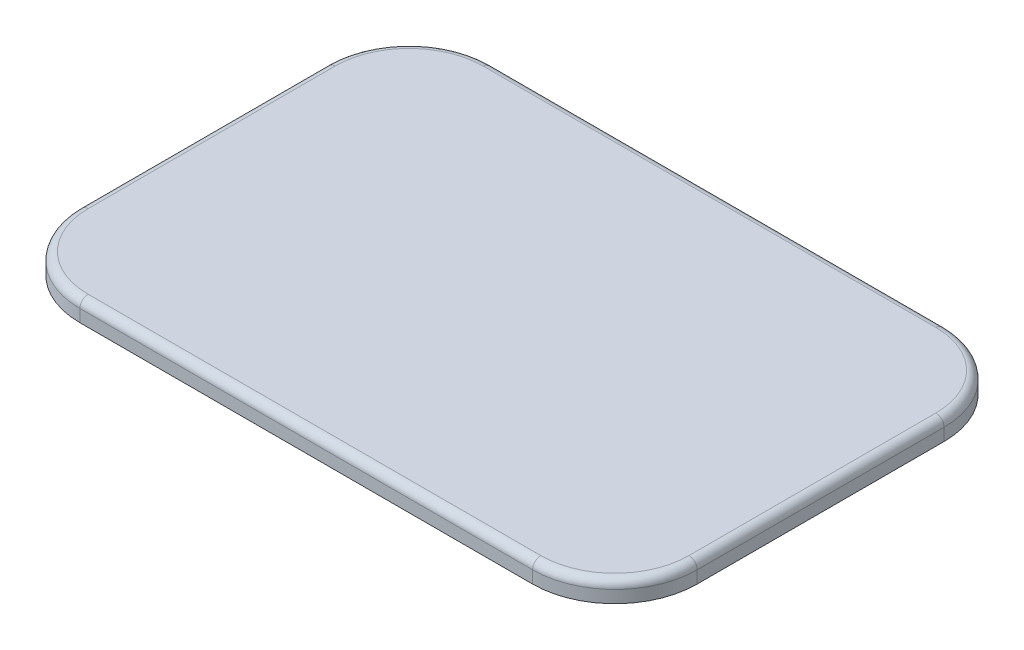
SolidWorks part; units mm, degrees
ref_plane "Płaszczyzna przednia" through (0, 0, 0) normal (0, 0, 1) x (1, 0, 0)
ref_plane "Płaszczyzna górna" through (0, 0, 0) normal (0, 1, 0) x (1, 0, 0)
ref_plane "Płaszczyzna prawa" through (0, 0, 0) normal (1, 0, 0) x (0, 0, -1)
sketch "Szkic1" plane through (0, 0, 0) normal (0, 1, 0) x (1, 0, 0)
  line L1 (-110, -100) -> (110, -100)
  line L2 (-150, -60) -> (-150, 60)
  line L3 (-110, 100) -> (110, 100)
  line L4 (150, -60) -> (150, 60)
  line L5 (-150, -100) -> (150, 100) construction
  line L6 (-150, 100) -> (150, -100) construction
  arc A0 (110, 100) -> (150, 60) centre (110, 60) cw
  arc A1 (110, -100) -> (150, -60) centre (110, -60) ccw
  arc A2 (-110, -100) -> (-150, -60) centre (-110, -60) cw
  arc A3 (-150, 60) -> (-110, 100) centre (-110, 60) cw
  point P0 (0, 0)
  dimension "D3" = 40
  dimension "D1" = 300
  dimension "D2" = 200
extrude "Dodanie-wyciągnięcie1" add sketch "Szkic1" along normal blind 10
fillet "Zaokrąglenie1" radius 4 8 edges at (-138.2843, 10, 88.2843) (-150, 10, 0) (-138.2843, 10, -88.2843) (0, 10, -100) (138.2843, 10, -88.2843) (150, 10, 0) (138.2843, 10, 88.2843) (0, 10, 100)
